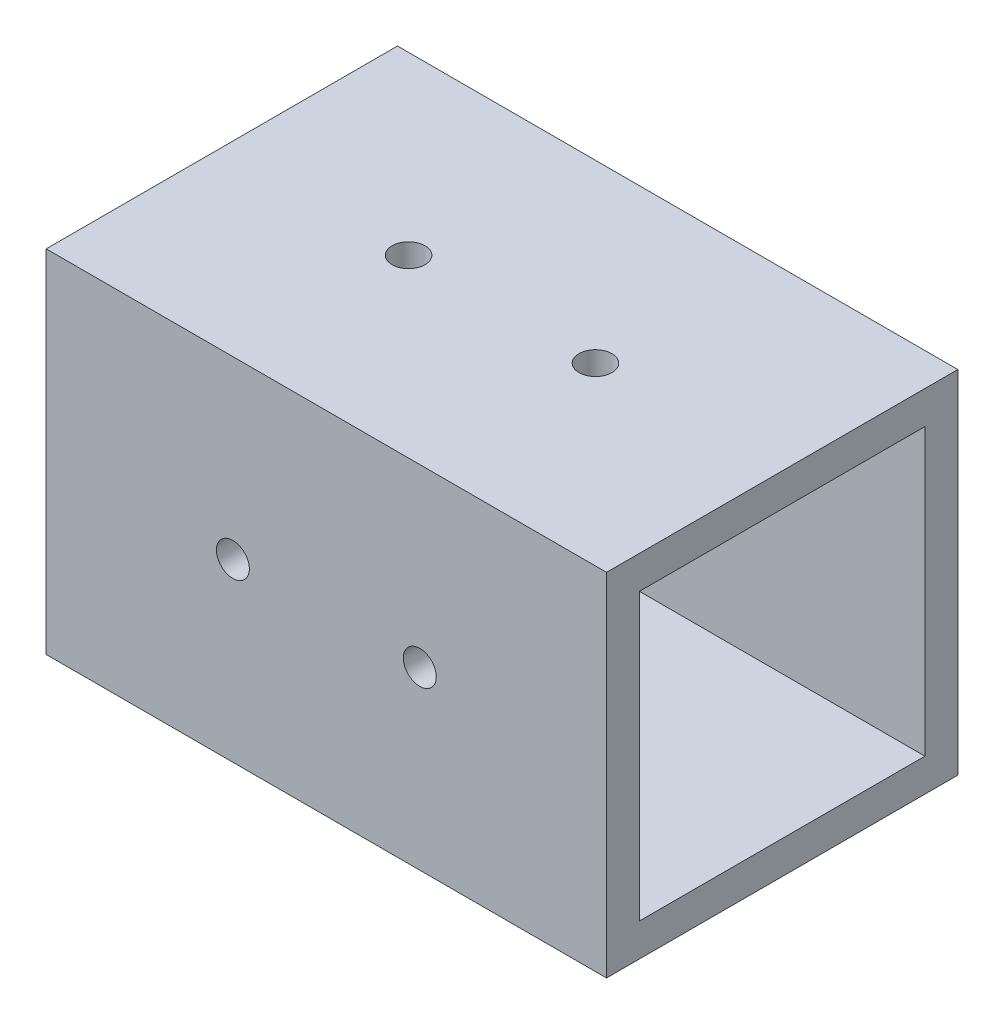
SolidWorks part; units mm, degrees
ref_plane "Front Plane" through (0, 0, 0) normal (0, 0, 1) x (1, 0, 0)
ref_plane "Top Plane" through (0, 0, 0) normal (0, 1, 0) x (1, 0, 0)
ref_plane "Right Plane" through (0, 0, 0) normal (1, 0, 0) x (0, 0, -1)
sketch "Sketch1" plane through (0, 0, 0) normal (1, 0, 0) x (0, 0, -1)
  line L0 (-4.7625, 4.7625) -> (-4.7625, 46.0375)
  line L1 (0, 0) -> (-50.8, 0)
  line L2 (0, 0) -> (0, 50.8)
  line L3 (0, 50.8) -> (-50.8, 50.8)
  line L4 (-50.8, 0) -> (-50.8, 50.8)
  line L5 (-4.7625, 46.0375) -> (-46.0375, 46.0375)
  line L6 (-46.0375, 4.7625) -> (-46.0375, 46.0375)
  line L7 (-4.7625, 4.7625) -> (-46.0375, 4.7625)
  dimension "D1" = 50.8
  dimension "D2" = 4.7625
extrude "Boss-Extrude1" add sketch "Sketch1" along normal blind 81.025
sketch "Sketch2" plane through (0, 0, 50.8) normal (0, 0, 1) x (1, 0, 0)
  line L0 (0, 50.8) -> (0, 0) construction
  line L2 (81.025, 50.8) -> (81.025, 0) construction
  circle A0 centre (27, 25.4) radius 2.3812
  circle A1 centre (54.025, 25.4) radius 2.3812
  point P5 (0, 25.4)
  dimension "D1" = 4.7625
  dimension "D2" = 27
  dimension "D3" = 27
extrude "Cut-Extrude1" cut sketch "Sketch2" against normal up to surface (50.8 mm away) up to face at (40.5125, 25.4, 0)
sketch "Sketch3" plane through (0, 0, 0) normal (0, -1, 0) x (1, 0, 0)
  line L0 (0, 50.8) -> (0, 0) construction
  line L1 (81.025, 50.8) -> (81.025, 0) construction
  circle A0 centre (27, 25.4) radius 2.3813
  circle A1 centre (54.025, 25.4) radius 2.3812
  point P9 (0, 25.4)
  dimension "D1" = 4.7625
  dimension "D2" = 27
  dimension "D3" = 27
extrude "Cut-Extrude2" cut sketch "Sketch3" against normal blind 52.324
